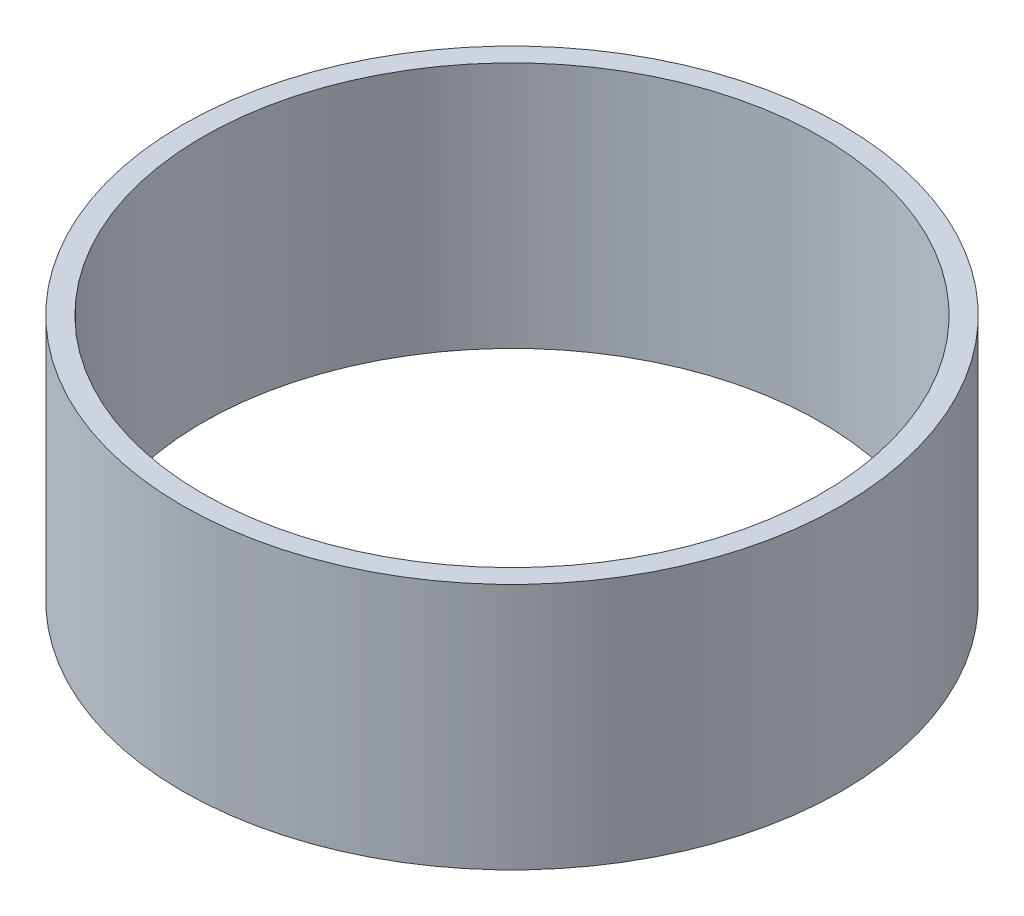
SolidWorks part; units mm, degrees
ref_plane "Alzado" through (0, 0, 0) normal (0, 0, 1) x (1, 0, 0)
ref_plane "Planta" through (0, 0, 0) normal (0, 1, 0) x (1, 0, 0)
ref_plane "Vista lateral" through (0, 0, 0) normal (1, 0, 0) x (0, 0, -1)
sketch "Croquis2" plane through (0, 0, 0) normal (0, 1, 0) x (1, 0, 0)
  circle A0 centre (0, 0) radius 40
  circle A1 centre (0, 0) radius 37.5
  dimension "D1" = 2.5
extrude "Saliente-Extruir1" add sketch "Croquis2" along normal blind 30
